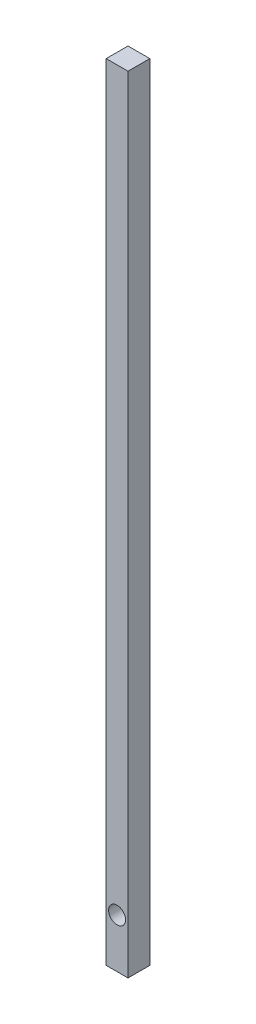
SolidWorks part; units mm, degrees
ref_plane "Front Plane" through (0, 0, 0) normal (0, 0, 1) x (1, 0, 0)
ref_plane "Top Plane" through (0, 0, 0) normal (0, 1, 0) x (1, 0, 0)
ref_plane "Right Plane" through (0, 0, 0) normal (1, 0, 0) x (0, 0, -1)
sketch "Sketch1" plane through (0, 0, 0) normal (0, 1, 0) x (1, 0, 0)
  line L1 (12.7, -12.7) -> (-12.7, -12.7)
  line L2 (12.7, -12.7) -> (12.7, 12.7)
  line L3 (12.7, 12.7) -> (-12.7, 12.7)
  line L4 (-12.7, -12.7) -> (-12.7, 12.7)
  line L5 (12.7, -12.7) -> (-12.7, 12.7) construction
  line L6 (12.7, 12.7) -> (-12.7, -12.7) construction
  point P0 (0, 0)
  dimension "D1" = 25.4
  dimension "D2" = 25.4
extrude "Boss-Extrude2" add sketch "Sketch1" along normal blind 914.4
sketch "Sketch2" plane through (0, 0, -12.7) normal (0, 0, -1) x (-1, 0, 0)
  line L0 (0, 0) -> (0, 57.15) construction
  circle A0 centre (0, 57.15) radius 9.906
  dimension "D1" = 57.15
extrude "Cut-Extrude1" cut sketch "Sketch2" against normal through all
